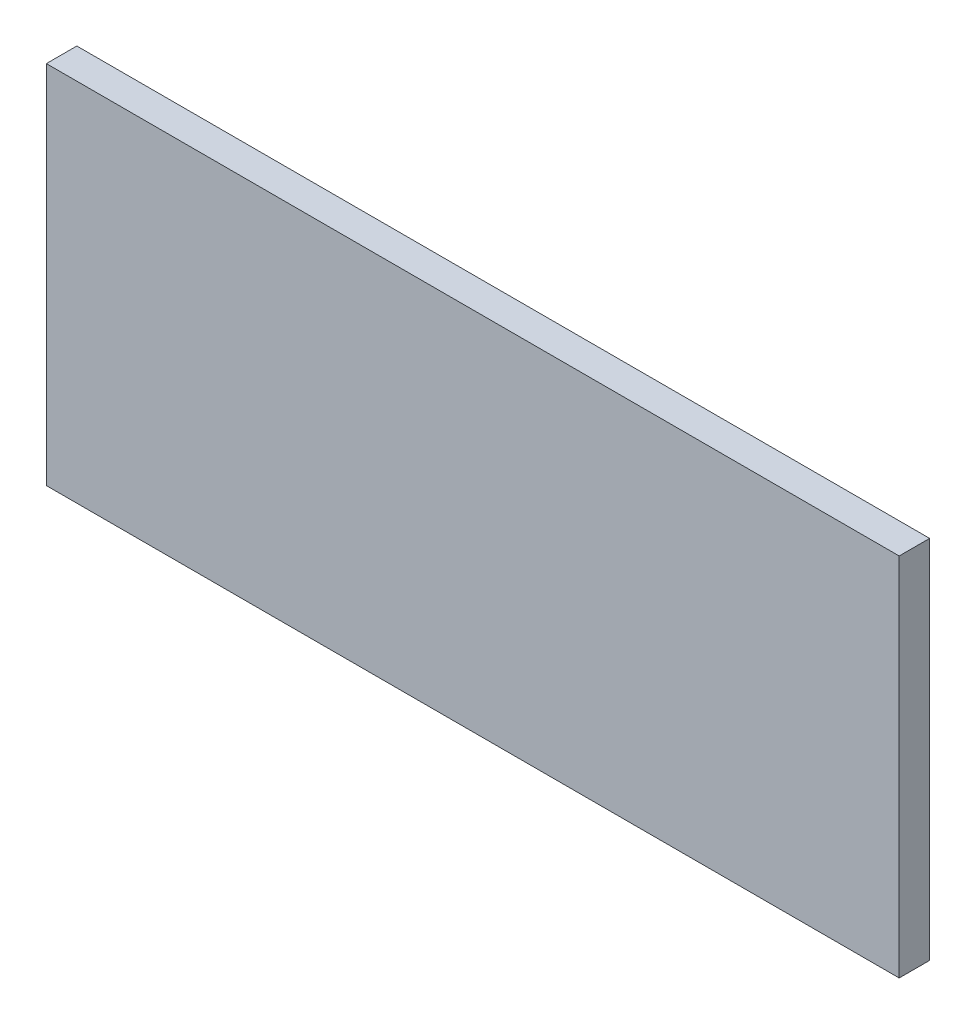
SolidWorks part; units mm, degrees
ref_plane "Front Plane" through (0, 0, 0) normal (0, 0, 1) x (1, 0, 0)
ref_plane "Top Plane" through (0, 0, 0) normal (0, 1, 0) x (1, 0, 0)
ref_plane "Right Plane" through (0, 0, 0) normal (1, 0, 0) x (0, 0, -1)
sketch "Sketch1" plane through (0, 0, 0) normal (0, 0, 1) x (1, 0, 0)
  line L1 (0, 0) -> (177.8, 0)
  line L2 (0, 0) -> (0, 76.2)
  line L3 (0, 76.2) -> (177.8, 76.2)
  line L4 (177.8, 0) -> (177.8, 76.2)
  dimension "D1" = 76.2
  dimension "D2" = 177.8
extrude "Boss-Extrude1" add sketch "Sketch1" along normal blind 6.35
